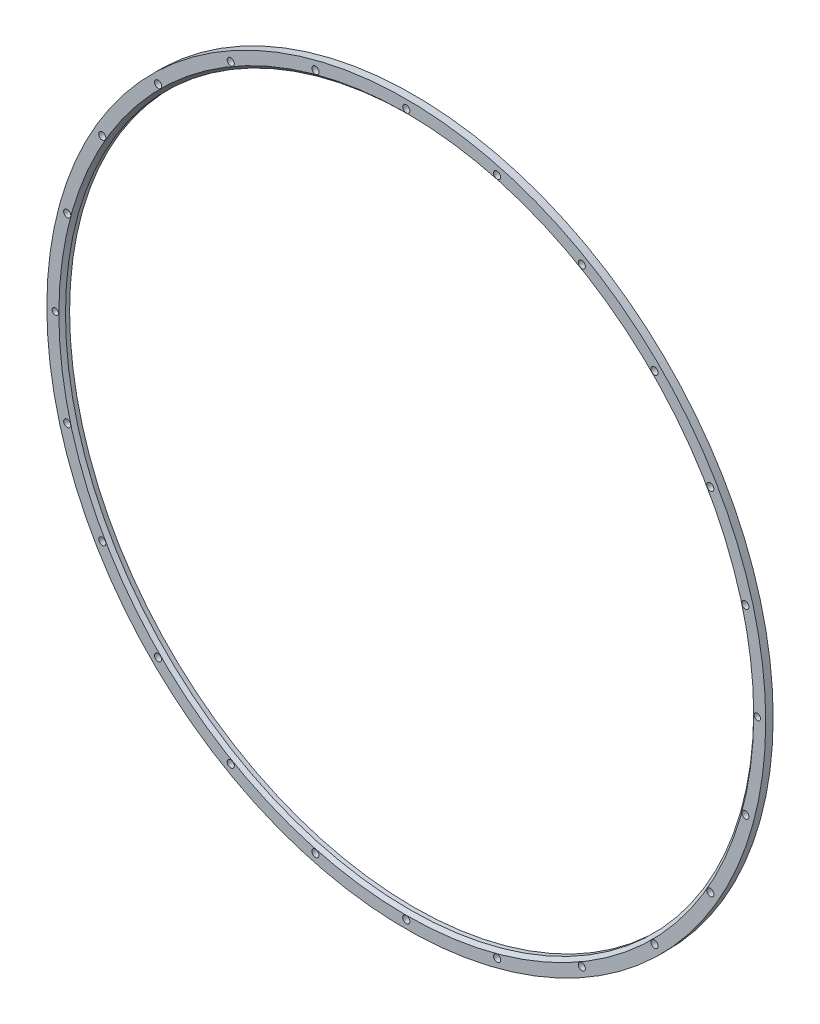
SolidWorks part; units mm, degrees
material "Isotropic CFRP"
ref_plane "Front Plane" through (0, 0, 0) normal (0, 0, 1) x (1, 0, 0)
ref_plane "Top Plane" through (0, 0, 0) normal (0, 1, 0) x (1, 0, 0)
ref_plane "Right Plane" through (0, 0, 0) normal (1, 0, 0) x (0, 0, -1)
sketch "Sketch1" plane through (0, 0, 0) normal (0, 0, 1) x (1, 0, 0)
  circle A0 centre (0, 0) radius 203.325
  circle A1 centre (0, 0) radius 227.325
  dimension "D1" = 454.65
  dimension "D2" = 24
  dimension "D3" = 406.65
extrude "Extrude1" add sketch "Sketch1" along normal blind 4.7
sketch "Sketch2" plane through (0, 0, 0) normal (0, 0, -1) x (-1, 0, 0)
  circle A3 centre (0, 0) radius 217.625
  dimension "D1" = 435.25
extrude "Extrude2" cut sketch "Sketch2" against normal through all
hole_wizard "M4 Clearance Hole1" positions "Sketch4" profile "Sketch5" hole size "M4" standard "Ansi Metric" end condition through all
sketch "Sketch4" plane through (0, 0, 4.7) normal (0, 0, 1) x (1, 0, 0)
  point P0 (0, 222)
  dimension "D1" = 222
sketch "Sketch5" plane through (0, 222, 4.7) normal (1, 0, 0) x (0, -1, 0)
  line L0 (0, 0) -> (0, 4.7)
  line L1 (0, 4.7) -> (2.25, 4.7)
  line L2 (2.25, 4.7) -> (2.25, 0)
  line L5 (2.25, 0) -> (0, 0)
  line L11 (0, -6.35) -> (0, 107.95) construction
  dimension "Thru Hole Dia." = 4.5
  dimension "Thru Hole Depth" = 4.7
sketch "Sketch6" plane through (0, 0, 4.7) normal (0, 0, -1) x (-1, 0, 0)
  line L0 (-3.15, 215) -> (3.15, 215)
  line L1 (-5.15, 217) -> (5.15, 217) construction
  line L2 (-5.15, 217) -> (-5.15, 232)
  line L3 (-5.15, 232) -> (5.15, 232)
  line L4 (5.15, 217) -> (5.15, 232)
  line L5 (0, 232) -> (0, 217) construction
  line L9 (5.15, 232) -> (-5.15, 232)
  arc A0 (-3.15, 215) -> (-5.15, 217) centre (-3.15, 217) cw
  arc A1 (3.15, 215) -> (5.15, 217) centre (3.15, 217) ccw
  point P0 (0, 222)
  circle M31 centre (0, 222) radius 2.25
  circle M32 centre (0, 0) radius 227.325
  dimension "D4" = 2
  dimension "D1" = 15
  dimension "D2" = 10.3
  dimension "D3" = 5
extrude "Cut-Extrude1" [suppressed] cut sketch "Sketch6" along normal blind 3.3 contours A1 L0 A0 L2 L4 M32 M31
hole_wizard "M4 Clearance Hole2" positions "Sketch8" profile "Sketch9" hole size "M4" standard "Ansi Metric"
sketch "Sketch8" plane through (0, 0, 4.7) normal (0, 0, 1) x (1, 0, 0)
  line L0 (0, 222) -> (0, 208) construction
  point P0 (0, 208)
  dimension "D1" = 14
sketch "Sketch9" plane through (0, 208, 4.7) normal (1, 0, 0) x (0, -1, 0)
  line L0 (0, 0) -> (0, 4.7)
  line L1 (0, 4.7) -> (2.15, 4.7)
  line L2 (2.15, 4.7) -> (2.15, 0)
  line L5 (2.15, 0) -> (0, 0)
  line L11 (0, -6.35) -> (0, 107.95) construction
  dimension "Thru Hole Dia." = 4.3
  dimension "Thru Hole Depth" = 5
pattern_circular "CirPattern1" count 24 over 360 about axis through (0, 0, 0) along (0, 0, 1) of "M4 Clearance Hole1", "Cut-Extrude1", "M4 Clearance Hole2"
sketch "Sketch10" [suppressed] plane through (0, 0, 4.7) normal (0, 0, 1) x (1, 0, 0)
  line L1 (215, 3.15) -> (215, -3.15) construction
  line L4 (-215, -3.15) -> (-215, 3.15) construction
  line L6 (226.9416, 5.15) -> (217, 5.15)
  line L7 (215, 3.15) -> (215, -3.15)
  line L8 (217, -5.15) -> (226.9416, -5.15)
  line L9 (-226.9416, -5.15) -> (-217, -5.15)
  line L10 (-215, -3.15) -> (-215, 3.15)
  line L11 (-217, 5.15) -> (-226.9416, 5.15)
  circle A0 centre (0, 208) radius 2
  circle A1 centre (208, 0) radius 2
  circle A2 centre (-208, 0) radius 2
  circle A3 centre (0, -208) radius 2
  circle A4 centre (0, -208) radius 2.15 construction
  circle A5 centre (208, 0) radius 2.15 construction
  circle A6 centre (0, 208) radius 2.15 construction
  circle A7 centre (-208, 0) radius 2.15 construction
  circle A8 centre (0, -208) radius 2.15
  circle A9 centre (208, 0) radius 2.15
  circle A10 centre (0, 208) radius 2.15
  circle A11 centre (-208, 0) radius 2.15
  circle A12 centre (-222, 0) radius 2
  circle A13 centre (222, 0) radius 2
  arc A14 (226.9416, -5.15) -> (226.9416, 5.15) centre (0, 0) ccw construction
  arc A15 (217, 5.15) -> (215, 3.15) centre (217, 3.15) ccw construction
  arc A16 (215, -3.15) -> (217, -5.15) centre (217, -3.15) ccw construction
  arc A17 (-226.9416, 5.15) -> (-226.9416, -5.15) centre (0, 0) ccw construction
  arc A18 (-217, -5.15) -> (-215, -3.15) centre (-217, -3.15) ccw construction
  arc A19 (-215, 3.15) -> (-217, 5.15) centre (-217, 3.15) ccw construction
  arc A20 (226.9416, -5.15) -> (226.9416, 5.15) centre (0, 0) ccw
  arc A21 (217, 5.15) -> (215, 3.15) centre (217, 3.15) ccw
  arc A22 (215, -3.15) -> (217, -5.15) centre (217, -3.15) ccw
  arc A23 (-226.9416, 5.15) -> (-226.9416, -5.15) centre (0, 0) ccw
  arc A24 (-217, -5.15) -> (-215, -3.15) centre (-217, -3.15) ccw
  arc A25 (-215, 3.15) -> (-217, 5.15) centre (-217, 3.15) ccw
  dimension "D1" = 4
extrude "Boss-Extrude1" [suppressed] add sketch "Sketch10" against normal up to surface (4.7 mm away)
sketch "Sketch11" plane through (0, 0, 4.7) normal (0, 0, 1) x (1, 0, 0)
  circle A0 centre (-222, 0) radius 2
  circle A1 centre (222, 0) radius 2
  circle A2 centre (222, 0) radius 2.25 construction
  circle A3 centre (-222, 0) radius 2.25 construction
  circle A4 centre (222, 0) radius 2.25
  circle A5 centre (-222, 0) radius 2.25
  dimension "D1" = 4
extrude "Boss-Extrude2" add sketch "Sketch11" against normal up to surface (4.7 mm away) up to face at (-55.2845, 215.0179, 0)
chamfer "Chamfer1" distance 2.1 angle 45 1 edges at (-217.625, 0, 4.7)
sketch "Sketch12" [suppressed] plane through (0, 0, 4.7) normal (0, 0, 1) x (1, 0, 0)
  circle A1 centre (0, 0) radius 227.325 construction
  circle A2 centre (0, 0) radius 227.325
  circle A3 centre (0, 0) radius 228.075
  dimension "D1" = 0.75
extrude "Boss-Extrude3 - INITIAL WATERJET EXTRA MATL ON OD" [suppressed] add sketch "Sketch12" against normal up to surface (4.7 mm away)
